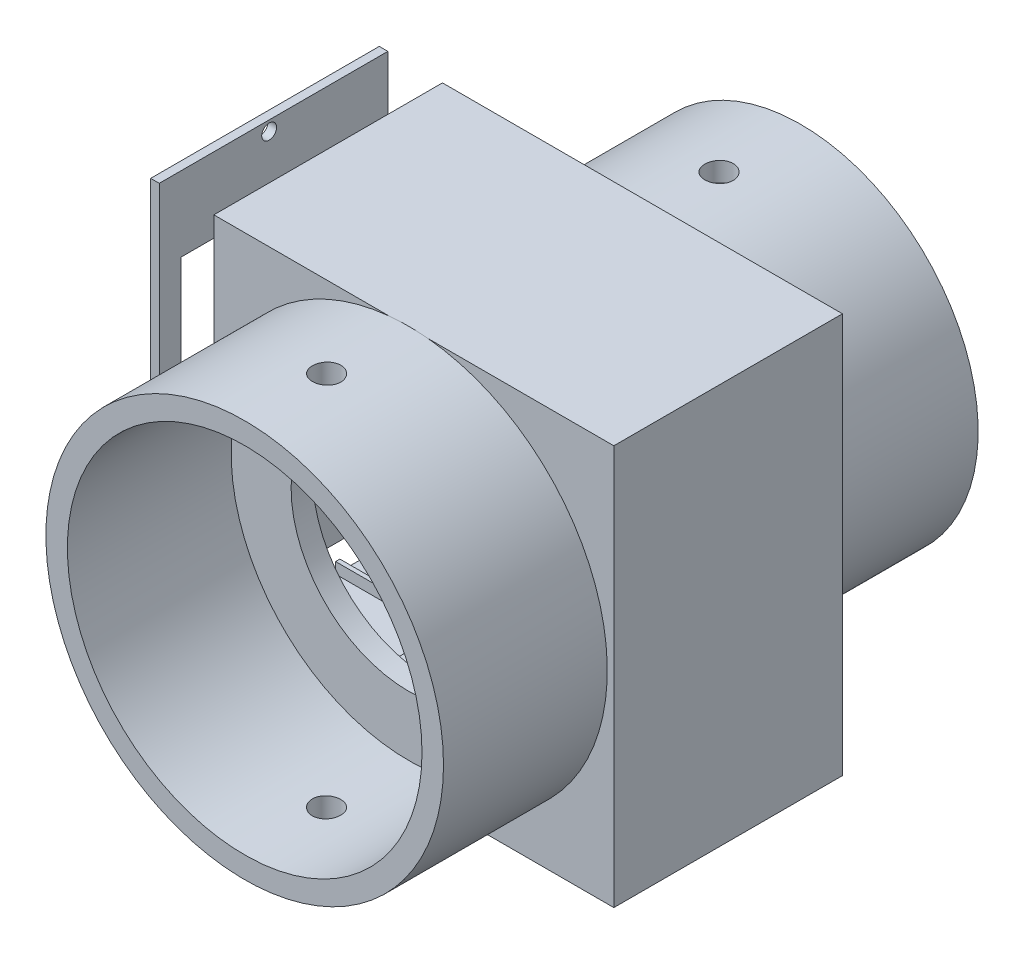
SolidWorks part; units mm, degrees
ref_plane "Front Plane" through (0, 0, 0) normal (0, 0, 1) x (1, 0, 0)
ref_plane "Top Plane" through (0, 0, 0) normal (0, 1, 0) x (1, 0, 0)
ref_plane "Right Plane" through (0, 0, 0) normal (1, 0, 0) x (0, 0, -1)
sketch "Sketch1" plane through (0, 0, 0) normal (0, 1, 0) x (1, 0, 0)
  line L1 (-73.7279, 22.6213) -> (8.8221, 22.6213)
  line L2 (-73.7279, 22.6213) -> (-73.7279, -20.5587)
  line L3 (-73.7279, -20.5587) -> (8.8221, -20.5587)
  line L4 (8.8221, 22.6213) -> (8.8221, -20.5587)
  line L5 (-73.7279, 22.6213) -> (8.8221, -20.5587) construction
  line L6 (-73.7279, -20.5587) -> (8.8221, 22.6213) construction
  point P0 (-32.4529, 1.0313)
  dimension "D1" = 82.55
  dimension "D2" = 43.18
extrude "Boss-Extrude1" add sketch "Sketch1" along normal blind 6.5
sketch "Sketch2" plane through (0, 6.5, 0) normal (0, 1, 0) x (1, 0, 0)
  line L0 (-32.4529, -20.5587) -> (-32.4529, 22.6213) construction
  line L1 (-73.7279, -20.5587) -> (8.8221, -20.5587) construction
  line L2 (8.8221, 22.6213) -> (-73.7279, 22.6213) construction
sketch "Sketch3" plane through (0, 6.5, 0) normal (0, 1, 0) x (1, 0, 0)
  line L0 (-37.5375, 20.6213) -> (-27.3682, 20.6213)
  line L1 (-27.3682, 20.6213) -> (-27.3682, 5.1273)
  line L2 (-27.3682, 5.1273) -> (-37.5375, 5.1273)
  line L3 (-37.5375, 5.1273) -> (-37.5375, 20.6213)
  line L4 (8.8221, 22.6213) -> (-73.7279, 22.6213) construction
  line L5 (-32.4529, -20.5587) -> (-32.4529, 22.6213) construction
  dimension "D1" = 2
  dimension "D2" = 15.494
  dimension "D3" = 5.0846
  dimension "D4" = 5.0846
extrude "Boss-Extrude2" add sketch "Sketch3" along normal blind 13.5433
sketch "Sketch4" plane through (0, 20.0433, 0) normal (0, 1, 0) x (1, 0, 0)
  line L0 (-27.3682, 12.3273) -> (-37.5375, 12.3273) construction
  line L1 (-27.3682, 5.1273) -> (-27.3682, 20.6213) construction
  line L2 (-37.5375, 20.6213) -> (-37.5375, 5.1273) construction
  line L3 (-37.5375, 5.1273) -> (-27.3682, 5.1273) construction
  dimension "D1" = 7.2
hole_wizard "Hole for #8 300® SC Nuts (SP)1" positions "Sketch7" profile "Sketch6" hole size "#8-32" standard "PEM® Inch" end condition up to next
sketch "Sketch7" plane through (0, 20.0433, 0) normal (0, 1, 0) x (1, 0, 0)
  line L0 (-27.3682, 12.3273) -> (-37.5375, 12.3273) construction
  point P0 (-32.4529, 12.3273)
sketch "Sketch6" plane through (-32.4529, 20.0433, -12.3273) normal (1, 0, 0) x (0, 0, 1)
  line L0 (0, 0) -> (0, 20.0433)
  line L1 (0, 20.0433) -> (2.7051, 20.0433)
  line L2 (2.7051, 20.0433) -> (2.7051, 0)
  line L5 (2.7051, 0) -> (0, 0)
  line L11 (0, -6.35) -> (0, 107.95) construction
  dimension "Thru Hole Dia." = 5.4102
  dimension "Thru Hole Depth" = 20.0433
sketch "Sketch8" plane through (0, 6.5, 0) normal (0, 1, 0) x (1, 0, 0)
  line L0 (-52.4661, 2.7613) -> (-15.4863, 2.7613)
  line L1 (-15.4863, 2.7613) -> (-15.4863, -17.5587)
  line L2 (-15.4863, -17.5587) -> (-52.4661, -17.5587)
  line L3 (-52.4661, -17.5587) -> (-52.4661, 2.7613)
  line L4 (-73.7279, -20.5587) -> (8.8221, -20.5587) construction
  line L5 (8.8221, -20.5587) -> (8.8221, 22.6213) construction
  dimension "D1" = 3
  dimension "D2" = 20.32
  dimension "D3" = 24.3085
  dimension "D4" = 61.2883
extrude "Boss-Extrude3" add sketch "Sketch8" along normal blind 1.275
sketch "Sketch9" plane through (0, 7.775, 0) normal (0, 1, 0) x (1, 0, 0)
  line L0 (-32.4529, -17.5587) -> (-32.4529, 2.7613) construction
  line L1 (-52.4661, -17.5587) -> (-15.4863, -17.5587) construction
  line L2 (-15.4863, 2.7613) -> (-52.4661, 2.7613) construction
  line L3 (-45.1529, -17.5587) -> (-45.1529, 2.7613) construction
  line L4 (-15.4863, -8.0587) -> (-52.4661, -8.0587) construction
  line L5 (-15.4863, -17.5587) -> (-15.4863, 2.7613) construction
  line L6 (-52.4661, 2.7613) -> (-52.4661, -17.5587) construction
  line L7 (8.8221, -20.5587) -> (8.8221, 22.6213) construction
  dimension "D1" = 9.5
  dimension "D2" = 41.275
  dimension "D3" = 12.7
hole_wizard "Hole for #8 300® SC Nuts (SP)2" positions "Sketch10" profile "Sketch11" hole size "#8-32" standard "PEM® Inch" end condition up to next
sketch "Sketch10" plane through (0, 7.775, 0) normal (0, 1, 0) x (1, 0, 0)
  line L0 (-32.4529, -20.5587) -> (-32.4529, 22.6213) construction
  line L1 (-15.4863, -8.0587) -> (-52.4661, -8.0587) construction
  line L2 (-45.1529, -17.5587) -> (-45.1529, 2.7613) construction
  point P0 (-32.4529, -8.0587)
  point P6 (-45.1529, -8.0587)
sketch "Sketch11" plane through (-32.4529, 7.775, 8.0587) normal (1, 0, 0) x (0, 0, 1)
  line L0 (0, 0) -> (0, 7.775)
  line L1 (0, 7.775) -> (2.7051, 7.775)
  line L2 (2.7051, 7.775) -> (2.7051, 0)
  line L5 (2.7051, 0) -> (0, 0)
  line L11 (0, -6.35) -> (0, 107.95) construction
  dimension "Thru Hole Dia." = 5.4102
  dimension "Thru Hole Depth" = 7.775
sketch "Sketch12" plane through (0, 0, 0) normal (0, -1, 0) x (-1, 0, 0)
  line L0 (-15.3221, -25.5587) -> (80.2279, -25.5587)
  line L1 (80.2279, -25.5587) -> (80.2279, 27.6213)
  line L2 (80.2279, 27.6213) -> (-15.3221, 27.6213)
  line L3 (-15.3221, 27.6213) -> (-15.3221, -25.5587)
  line L4 (-8.8221, -20.5587) -> (-8.8221, 22.6213) construction
  line L5 (-8.8221, 22.6213) -> (73.7279, 22.6213) construction
  line L6 (73.7279, 22.6213) -> (73.7279, -20.5587) construction
  line L7 (73.7279, -20.5587) -> (-8.8221, -20.5587) construction
  dimension "D1" = 6.5
  dimension "D2" = 5
  dimension "D3" = 6.5
  dimension "D4" = 5
sketch "Sketch14" plane through (0, 0, 0) normal (0, -1, 0) x (-1, 0, 0)
  line L0 (73.7279, 22.6213) -> (73.7279, 27.6213)
  line L1 (80.2279, 27.6213) -> (-15.3221, 27.6213) construction
  line L2 (73.7279, 27.6213) -> (-8.8221, 27.6213)
  line L3 (-8.8221, 27.6213) -> (-8.8221, 22.6213)
  line L4 (-8.8221, 22.6213) -> (73.7279, 22.6213)
extrude "Boss-Extrude5" add sketch "Sketch14" against normal blind 87.55
sketch "Sketch16" plane through (0, 0, 0) normal (0, -1, 0) x (-1, 0, 0)
  line L0 (-15.3221, 27.6213) -> (-15.3221, -25.5587)
  line L1 (-15.3221, -25.5587) -> (-8.8221, -25.5587)
  line L2 (-15.3221, -25.5587) -> (80.2279, -25.5587) construction
  line L3 (-8.8221, -25.5587) -> (-8.8221, 27.6213)
  line L4 (-8.8221, 27.6213) -> (-15.3221, 27.6213)
extrude "Boss-Extrude6" add sketch "Sketch16" against normal blind 87.55
sketch "Sketch17" plane through (0, 0, 0) normal (0, -1, 0) x (-1, 0, 0)
  line L0 (-8.8221, -25.5587) -> (80.2279, -25.5587)
  line L1 (80.2279, -25.5587) -> (80.2279, -20.5587)
  line L2 (80.2279, -25.5587) -> (80.2279, 27.6213) construction
  line L3 (80.2279, -20.5587) -> (-8.8221, -20.5587)
  line L4 (-8.8221, -20.5587) -> (-8.8221, -25.5587)
sketch "Sketch19" plane through (0, 0, 0) normal (0, -1, 0) x (1, 0, 0)
  line L0 (-73.7279, 20.5587) -> (-73.7279, 25.5587)
  line L1 (15.3221, 25.5587) -> (-80.2279, 25.5587) construction
  line L2 (-73.7279, 25.5587) -> (8.8221, 25.5587)
  line L3 (8.8221, 25.5587) -> (8.8221, 20.5587)
  line L4 (8.8221, 20.5587) -> (-73.7279, 20.5587)
extrude "Boss-Extrude9" add sketch "Sketch19" against normal blind 87.55
sketch "Sketch20" plane through (0, 0, -22.6213) normal (0, 0, 1) x (1, 0, 0)
  line L0 (8.8221, 47.025) -> (-73.7279, 47.025) construction
  line L1 (8.8221, 87.55) -> (8.8221, 6.5) construction
  line L2 (-73.7279, 87.55) -> (-73.7279, 0) construction
  line L3 (-32.4529, 6.5) -> (-32.4529, 87.55) construction
  line L4 (8.8221, 6.5) -> (-73.7279, 6.5) construction
  line L5 (-73.7279, 87.55) -> (15.3221, 87.55) construction
  circle A0 centre (-32.4529, 47.025) radius 27.305
extrude "Cut-Extrude1" cut sketch "Sketch20" along normal through all and the other way through all
sketch "Sketch21" plane through (0, 87.55, 0) normal (0, 1, 0) x (1, 0, 0)
  line L0 (-73.7279, 27.6213) -> (-73.7279, -25.5587)
  line L1 (-73.7279, -25.5587) -> (15.3221, -25.5587)
  line L2 (15.3221, -25.5587) -> (15.3221, 27.6213)
  line L3 (15.3221, 27.6213) -> (-73.7279, 27.6213)
extrude "Boss-Extrude10" add sketch "Sketch21" along normal blind 5.5
sketch "Sketch25" plane through (-73.7279, 0, 0) normal (-1, 0, 0) x (0, 0, 1)
  line L0 (-27.6213, 93.05) -> (25.5587, 93.05)
  line L1 (25.5587, 93.05) -> (25.5587, 0)
  line L2 (25.5587, 0) -> (-27.6213, 0)
  line L3 (-27.6213, 93.05) -> (-27.6213, 0) construction
  line L4 (-27.6213, 0) -> (-27.6213, 93.05)
  line L5 (-22.6213, 87.55) -> (20.5587, 87.55)
  line L6 (20.5587, 87.55) -> (20.5587, 6.5)
  line L7 (20.5587, 6.5) -> (-22.6213, 6.5)
  line L8 (-22.6213, 6.5) -> (-22.6213, 87.55)
extrude "Boss-Extrude11" add sketch "Sketch25" along normal blind 4
sketch "Sketch26" plane through (0, 0, 25.5587) normal (0, 0, 1) x (1, 0, 0)
  circle A0 centre (-32.4529, 47.025) radius 46.25
  circle A1 centre (-32.4529, 47.025) radius 41.25
extrude "Boss-Extrude12" add sketch "Sketch26" along normal blind 38.1
sketch "Sketch27" plane through (0, 0, -27.6213) normal (0, 0, -1) x (-1, 0, 0)
  circle A0 centre (32.4529, 47.025) radius 41.25
  circle A1 centre (32.4529, 47.025) radius 36.75
extrude "Boss-Extrude13" add sketch "Sketch27" along normal blind 38.1
ref_plane "Plane1" through (0, 88.275, 0) normal (0, 1, 0) x (1, 0, 0)
sketch "Sketch29" plane through (0, 88.275, 0) normal (0, 1, 0) x (1, 0, 0)
  line L0 (8.7971, 46.6713) -> (-32.4529, 46.6713) construction
  line L1 (8.7971, 27.6213) -> (8.7971, 65.7213) construction
hole_wizard "M6 Clearance Hole1" positions "Sketch30" profile "Sketch31" hole size "M6" standard "ANSI Metric" end condition through all
sketch "Sketch30" plane through (0, 88.275, 0) normal (0, 1, 0) x (1, 0, 0)
  point P0 (-32.4529, 46.6713)
sketch "Sketch31" plane through (-32.4529, 88.275, -46.6713) normal (1, 0, 0) x (0, 0, 1)
  line L0 (0, 0) -> (0, 88.275)
  line L1 (0, 88.275) -> (3.3, 88.275)
  line L2 (3.3, 88.275) -> (3.3, 0)
  line L5 (3.3, 0) -> (0, 0)
  line L11 (0, -6.35) -> (0, 107.95) construction
  dimension "Thru Hole Dia." = 6.6
  dimension "Thru Hole Depth" = 88.275
ref_plane "Plane2" through (0, 93.275, 0) normal (0, 1, 0) x (1, 0, 0)
sketch "Sketch32" plane through (0, 93.275, 0) normal (0, 1, 0) x (1, 0, 0)
  line L0 (13.7971, -44.6087) -> (-32.4529, -44.6087) construction
  line L1 (13.7971, -63.6587) -> (13.7971, -25.5587) construction
hole_wizard "M6 Clearance Hole2" positions "Sketch33" profile "Sketch34" hole size "M6" standard "ANSI Metric" end condition through all
sketch "Sketch33" plane through (0, 93.275, 0) normal (0, 1, 0) x (1, 0, 0)
  point P0 (-32.4529, -44.6087)
sketch "Sketch34" plane through (-32.4529, 93.275, 44.6087) normal (1, 0, 0) x (0, 0, 1)
  line L0 (0, 0) -> (0, 93.275)
  line L1 (0, 93.275) -> (3.3, 93.275)
  line L2 (3.3, 93.275) -> (3.3, 0)
  line L5 (3.3, 0) -> (0, 0)
  line L11 (0, -6.35) -> (0, 107.95) construction
  dimension "Thru Hole Dia." = 6.6
  dimension "Thru Hole Depth" = 93.275
sketch "Sketch35" plane through (0, 6.5, 0) normal (0, 1, 0) x (1, 0, 0)
  line L0 (-77.7279, 2.7613) -> (8.8221, 2.7613)
  line L1 (-77.7279, 27.6213) -> (-77.7279, -25.5587) construction
  line L2 (8.8221, -20.5587) -> (8.8221, 22.6213) construction
  line L3 (8.8221, 3.7613) -> (-77.7279, 3.7613)
  line L4 (-77.7279, 3.7613) -> (-77.7279, 2.7613)
  line L9 (8.8221, -20.5587) -> (8.8221, 22.6213)
  line L10 (8.8221, 22.6213) -> (-77.7279, 22.6213)
  line L11 (-77.7279, 22.6213) -> (-77.7279, -20.5587)
  line L12 (-77.7279, -20.5587) -> (8.8221, -20.5587)
  line L13 (8.8221, 2.7613) -> (8.8221, 3.7613)
  dimension "D2" = 1
  dimension "D1" = 0
extrude "Boss-Extrude14" add sketch "Sketch35" along normal blind 2.54
sketch "Sketch37" plane through (0, 6.5, 0) normal (0, 1, 0) x (1, 0, 0)
  line L1 (-80.2279, -20.5587) -> (8.8221, -20.5587) construction
  line L6 (8.8221, -18.8321) -> (8.8221, -19.8321)
  line L7 (8.8221, -20.5587) -> (8.8221, 22.6213) construction
  line L8 (8.8221, -19.8321) -> (-77.7279, -19.8321)
  line L9 (-77.7279, -25.5587) -> (-77.7279, 27.6213) construction
  line L10 (-77.7279, -19.8321) -> (-77.7279, -18.8321)
  line L11 (-77.7279, -18.8321) -> (8.8221, -18.8321)
  dimension "D1" = 1
  dimension "D2" = 1.7267
extrude "Boss-Extrude15" add sketch "Sketch37" along normal blind 2.54
sketch "Sketch38" plane through (-77.7279, 0, 0) normal (-1, 0, 0) x (0, 0, 1)
  line L0 (-27.6213, 93.05) -> (-27.6213, 0)
  line L1 (-27.6213, 0) -> (25.5587, 0)
  line L2 (25.5587, 0) -> (25.5587, 93.05)
  line L3 (25.5587, 93.05) -> (-27.6213, 93.05)
  line L4 (-4.6889, 6.5) -> (20.5587, 6.5)
  line L5 (20.5587, 6.5) -> (-22.6213, 6.5) construction
  line L6 (20.5587, 6.5) -> (20.5587, 75.6456)
  line L7 (20.5587, 6.5) -> (20.5587, 87.55) construction
  line L8 (20.5587, 75.6456) -> (-4.0723, 75.6456)
  line L9 (-4.0723, 75.6456) -> (-4.6889, 6.5)
  line L10 (-22.6213, 87.55) -> (-22.6213, 6.5) construction
  line L11 (20.5587, 87.55) -> (-22.6213, 87.55) construction
  dimension "D1" = 18.549
  dimension "D2" = 11.9044
ref_plane "Plane3" through (-90.4279, 0, 0) normal (-1, 0, 0) x (0, 0, 1)
sketch "Sketch39" plane through (-90.4279, 0, 0) normal (-1, 0, 0) x (0, 0, 1)
  line L0 (-27.6213, 93.05) -> (-27.6213, 0)
  line L1 (-27.6213, 0) -> (25.5587, 0)
  line L2 (25.5587, 0) -> (25.5587, 93.05)
  line L3 (25.5587, 93.05) -> (-27.6213, 93.05)
  line L4 (-4.0723, 75.6456) -> (-4.6889, 6.5)
  line L5 (-4.6889, 6.5) -> (20.5587, 6.5)
  line L6 (20.5587, 6.5) -> (20.5587, 75.6456)
  line L7 (20.5587, 75.6456) -> (-4.0723, 75.6456)
extrude "Boss-Extrude17" add sketch "Sketch39" along normal blind 2 separate body
hole_wizard "Tap Drill for #8-32 Tap2" positions "Sketch43" profile "Sketch44" hole size "#8-32" standard "ANSI Inch"
sketch "Sketch43" plane through (-92.4279, 0, 0) normal (-1, 0, 0) x (0, 0, 1)
  point P0 (0, 90.6962)
  point P2 (23.0457, 41.0728)
  point P4 (-25.2892, 41.0728)
  point P6 (0, 2.3538)
sketch "Sketch44" plane through (-92.4279, 90.6962, 0) normal (0, 1, 0) x (0, 0, 1)
  line L0 (0, 0) -> (0, 21.3578)
  line L1 (0, 21.3578) -> (1.7272, 20.32)
  line L2 (1.7272, 20.32) -> (1.7272, 0)
  line L5 (1.7272, 0) -> (0, 0)
  line L10 (0, 21.3578) -> (-1.7272, 20.32) construction
  line L11 (0, -6.35) -> (0, 107.95) construction
  dimension "Hole Dia." = 3.4544
  dimension "Hole Depth" = 20.32
  dimension "Drill Angle" = 118
